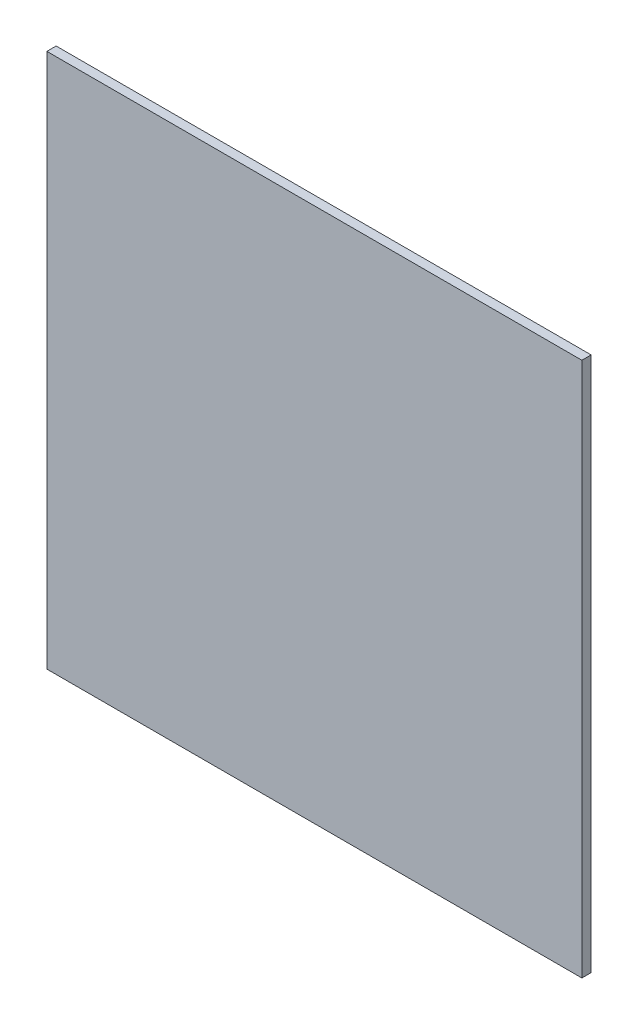
SolidWorks part; units mm, degrees
ref_plane "Front Plane" through (0, 0, 0) normal (0, 0, 1) x (1, 0, 0)
ref_plane "Top Plane" through (0, 0, 0) normal (0, 1, 0) x (1, 0, 0)
ref_plane "Right Plane" through (0, 0, 0) normal (1, 0, 0) x (0, 0, -1)
sketch "Sketch1" plane through (0, 0, 0) normal (0, 0, 1) x (1, 0, 0)
  line L1 (-550, -550) -> (550, -550)
  line L2 (-550, -550) -> (-550, 550)
  line L3 (-550, 550) -> (550, 550)
  line L4 (550, -550) -> (550, 550)
  line L5 (-550, -550) -> (550, 550) construction
  line L6 (-550, 550) -> (550, -550) construction
  point P0 (0, 0)
  dimension "D1" = 1100
extrude "Boss-Extrude1" add sketch "Sketch1" along normal blind 19.05
